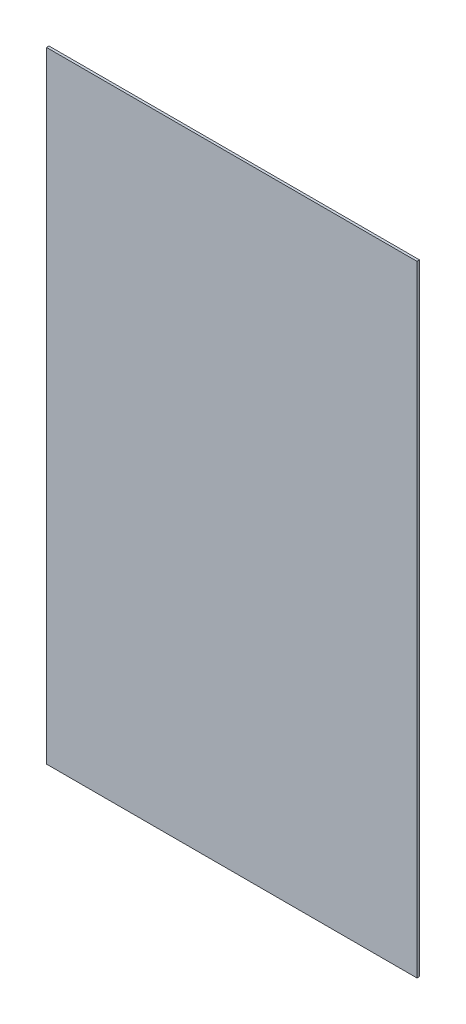
SolidWorks part; units mm, degrees
material "Plain Carbon Steel"
ref_plane "Front Plane" through (0, 0, 0) normal (0, 0, 1) x (1, 0, 0)
ref_plane "Top Plane" through (0, 0, 0) normal (0, 1, 0) x (1, 0, 0)
ref_plane "Right Plane" through (0, 0, 0) normal (1, 0, 0) x (0, 0, -1)
sketch "Sketch1" plane through (0, 0, 0) normal (0, 0, 1) x (1, 0, 0)
  line L0 (211.9633, 179.6979) -> (201.9633, 179.6979) construction
  line L1 (211.9633, 278.6979) -> (-84.0367, 278.6979)
  line L2 (211.9633, 278.6979) -> (211.9633, -217.3021)
  line L3 (211.9633, -217.3021) -> (-84.0367, -217.3021)
  line L4 (-84.0367, 278.6979) -> (-84.0367, -217.3021)
  line L11 (-84.0367, 278.6979) -> (211.9633, 278.6979) construction
  line L32 (211.9633, 179.6979) -> (-84.0367, 179.6979) construction
  point P0 (0, 0)
  point P12 (137.9633, 229.1979)
  point P19 (137.9633, 130.1979)
  dimension "D1" = 296
  dimension "D2" = 496
  dimension "D3" = 99
extrude "Boss-Extrude1" add sketch "Sketch1" along normal blind 2
